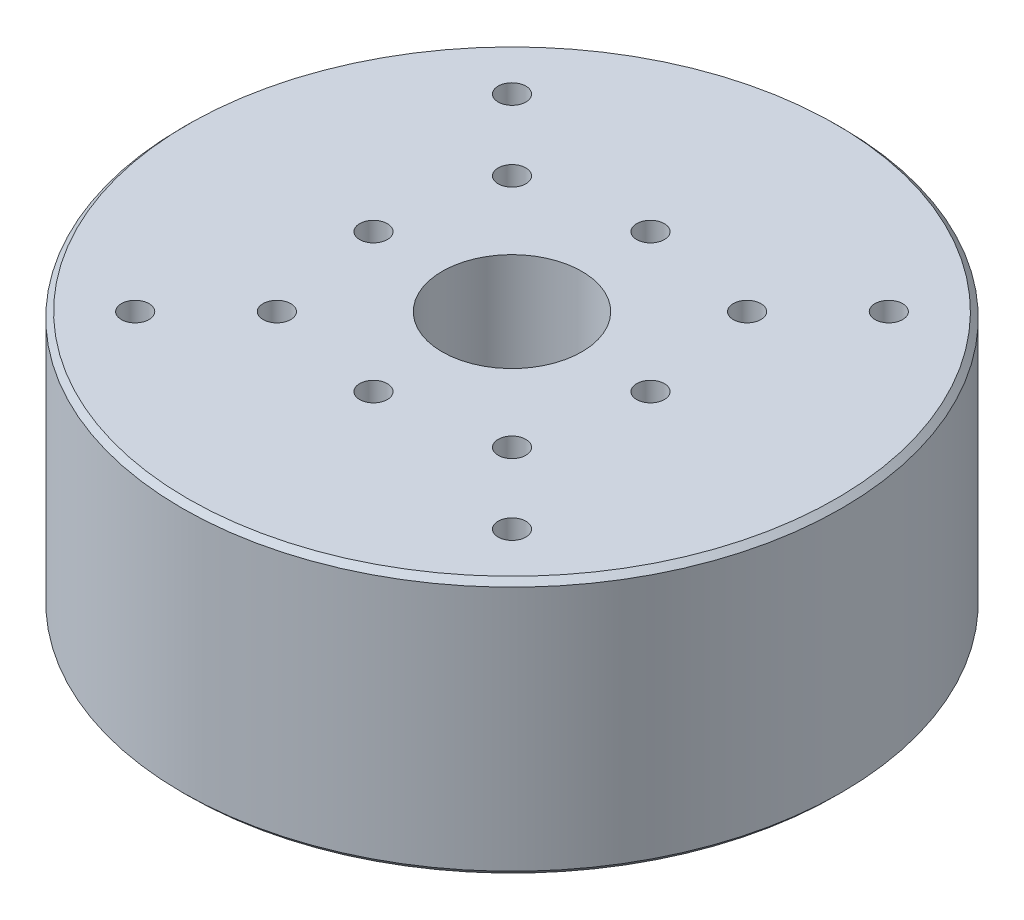
SolidWorks part; units mm, degrees
ref_plane "Front Plane" through (0, 0, 0) normal (0, 0, 1) x (1, 0, 0)
ref_plane "Top Plane" through (0, 0, 0) normal (0, 1, 0) x (1, 0, 0)
ref_plane "Right Plane" through (0, 0, 0) normal (1, 0, 0) x (0, 0, -1)
sketch "Sketch1" plane through (0, 0, 0) normal (0, 1, 0) x (1, 0, 0)
  circle A0 centre (0, 0) radius 29.75
  dimension "D1" = 59.5
extrude "Boss-Extrude1" add sketch "Sketch1" along normal blind 23.2
sketch "Sketch2" plane through (0, 23.2, 0) normal (0, 1, 0) x (1, 0, 0)
  circle A0 centre (0, 0) radius 6.3
  dimension "D1" = 12.6
extrude "Cut-Extrude1" cut sketch "Sketch2" against normal blind 20.5
sketch "Sketch3" plane through (0, 0, 0) normal (0, -1, 0) x (1, 0, 0)
  circle A0 centre (0, 0) radius 4.75
  dimension "D1" = 9.5
extrude "Cut-Extrude2" cut sketch "Sketch3" against normal up to surface (2.7 mm away) up to face at (0, 2.7, 6.3)
chamfer "Chamfer1" distance 0.5 angle 45 2 edges at (0, 0, 29.75) (0, 23.2, 29.75)
hole_wizard "M3x0.5 Tapped Hole1" positions "Sketch4" profile "Sketch5" tap size "M3x0.5" standard "ANSI Metric"
sketch "Sketch4" plane through (0, 0, 0) normal (0, -1, 0) x (-1, 0, 0)
  line L0 (0, 0) -> (0, 22) construction
  point P2 (0, 22)
  dimension "D1" = 22
sketch "Sketch5" plane through (0, 0, -22) normal (1, 0, 0) x (0, 0, -1)
  line L0 (0, 0) -> (0, 5.7511)
  line L1 (0, 5.7511) -> (1.25, 5)
  line L2 (1.25, 5) -> (1.25, 0)
  line L5 (1.25, 0) -> (0, 0)
  line L10 (0, 5.7511) -> (-1.25, 5) construction
  line L11 (0, -6.35) -> (0, 107.95) construction
  dimension "Tap Drill Dia." = 2.5
  dimension "Tap Drill Depth" = 5
  dimension "Drill Angle" = 118
cosmetic thread "Hole Thread1" parameters "D1"=6, "D2"=3
pattern_circular "CirPattern1" count 7 every 45 about axis through (0, 0, 0) along (0, 1, 0) of "M3x0.5 Tapped Hole1"
cosmetic thread "Hole Thread2" parameters "D1"=6, "D2"=3
cosmetic thread "Hole Thread3" parameters "D1"=6, "D2"=3
cosmetic thread "Hole Thread4" parameters "D1"=6, "D2"=3
cosmetic thread "Hole Thread5" parameters "D1"=6, "D2"=3
cosmetic thread "Hole Thread6" parameters "D1"=6, "D2"=3
cosmetic thread "Hole Thread7" parameters "D1"=6, "D2"=3
hole_wizard "M3x0.5 Tapped Hole2" positions "Sketch6" profile "Sketch7" tap size "M3x0.5" standard "ANSI Metric"
sketch "Sketch6" plane through (0, 0, 0) normal (0, -1, 0) x (-1, 0, 0)
  line L0 (0, 0) -> (8.8388, 8.8388) construction
  line L2 (0, 0) -> (14.7072, 0) construction
  point P2 (8.8388, 8.8388)
  dimension "D1" = 12.5
  dimension "D2" = 45
sketch "Sketch7" plane through (-8.8388, 0, -8.8388) normal (1, 0, 0) x (0, 0, -1)
  line L0 (0, 0) -> (0, 5.7511)
  line L1 (0, 5.7511) -> (1.25, 5)
  line L2 (1.25, 5) -> (1.25, 0)
  line L5 (1.25, 0) -> (0, 0)
  line L10 (0, 5.7511) -> (-1.25, 5) construction
  line L11 (0, -6.35) -> (0, 107.95) construction
  dimension "Tap Drill Dia." = 2.5
  dimension "Tap Drill Depth" = 5
  dimension "Drill Angle" = 118
cosmetic thread "Hole Thread8" parameters "D1"=6, "D2"=3
pattern_circular "CirPattern2" count 4 every 90 about axis through (0, 0, 0) along (0, 1, 0) of "M3x0.5 Tapped Hole2"
cosmetic thread "Hole Thread9" parameters "D1"=6, "D2"=3
cosmetic thread "Hole Thread10" parameters "D1"=6, "D2"=3
cosmetic thread "Hole Thread11" parameters "D1"=6, "D2"=3
hole_wizard "M3x0.5 Tapped Hole3" positions "Sketch8" profile "Sketch9" tap size "M3x0.5" standard "ANSI Metric"
sketch "Sketch8" plane through (0, 0, 0) normal (0, -1, 0) x (-1, 0, 0)
  line L0 (0, 0) -> (15, 0) construction
  point P0 (15, 0)
  dimension "D1" = 15
sketch "Sketch9" plane through (-15, 0, 0) normal (1, 0, 0) x (0, 0, -1)
  line L0 (0, 0) -> (0, 5.7511)
  line L1 (0, 5.7511) -> (1.25, 5)
  line L2 (1.25, 5) -> (1.25, 0)
  line L5 (1.25, 0) -> (0, 0)
  line L10 (0, 5.7511) -> (-1.25, 5) construction
  line L11 (0, -6.35) -> (0, 107.95) construction
  dimension "Tap Drill Dia." = 2.5
  dimension "Tap Drill Depth" = 5
  dimension "Drill Angle" = 118
cosmetic thread "Hole Thread12" parameters "D1"=6, "D2"=3
pattern_circular "CirPattern3" count 4 every 90 about axis through (0, 0, 0) along (0, 1, 0) of "M3x0.5 Tapped Hole3"
cosmetic thread "Hole Thread13" parameters "D1"=6, "D2"=3
cosmetic thread "Hole Thread14" parameters "D1"=6, "D2"=3
cosmetic thread "Hole Thread15" parameters "D1"=6, "D2"=3
sketch "Sketch10" plane through (0, 0, 0) normal (0, -1, 0) x (1, 0, 0)
  line L0 (-20.1166, -13.8158) -> (-13.0455, -20.8869)
  line L1 (-13.0455, -20.8869) -> (-15.8739, -23.7153)
  line L2 (-15.8739, -23.7153) -> (-22.945, -16.6442)
  line L3 (-22.945, -16.6442) -> (-20.1166, -13.8158)
  line L4 (-16.581, -17.3514) -> (0, 0) construction
  point P7 (-16.5412, -22.1766)
  dimension "D1" = 10
  dimension "D2" = 4
  dimension "D3" = 24
extrude "Cut-Extrude3" cut sketch "Sketch10" against normal blind 5
fillet "Fillet1" radius 0.5 4 edges at (-13.0455, 2.5, -20.8869) (-20.1166, 2.5, -13.8158) (-22.945, 2.5, -16.6442) (-15.8739, 2.5, -23.7153)
hole_wizard "M3x0.5 Tapped Hole4" positions "Sketch11" profile "Sketch12" tap size "M3x0.5" standard "ANSI Metric"
sketch "Sketch11" plane through (0, 23.2, 0) normal (0, 1, 0) x (1, 0, 0)
  line L0 (17, -17) -> (17, 17) construction
  line L1 (17, 17) -> (-17, 17) construction
  line L2 (-17, 17) -> (-17, -17) construction
  line L3 (-17, -17) -> (17, -17) construction
  line L5 (17, -17) -> (-17, 17) construction
  point P0 (-17, 17)
  point P2 (-17, -17)
  point P4 (17, -17)
  point P6 (17, 17)
  point P24 (0, 0)
  dimension "D1" = 34
  dimension "D2" = 34
sketch "Sketch12" plane through (-17, 23.2, -17) normal (1, 0, 0) x (0, 0, 1)
  line L0 (0, 0) -> (0, 5.7511)
  line L1 (0, 5.7511) -> (1.25, 5)
  line L2 (1.25, 5) -> (1.25, 0)
  line L5 (1.25, 0) -> (0, 0)
  line L10 (0, 5.7511) -> (-1.25, 5) construction
  line L11 (0, -6.35) -> (0, 107.95) construction
  dimension "Tap Drill Dia." = 2.5
  dimension "Tap Drill Depth" = 5
  dimension "Drill Angle" = 118
cosmetic thread "Hole Thread16" parameters "D1"=6, "D2"=3
cosmetic thread "Hole Thread17" parameters "D1"=6, "D2"=3
cosmetic thread "Hole Thread18" parameters "D1"=6, "D2"=3
cosmetic thread "Hole Thread19" parameters "D1"=6, "D2"=3
hole_wizard "M3x0.5 Tapped Hole5" positions "Sketch13" profile "Sketch14" tap size "M3x0.5" standard "ANSI Metric"
sketch "Sketch13" plane through (0, 23.2, 0) normal (0, 1, 0) x (1, 0, 0)
  line L0 (0, 0) -> (12.5, 0) construction
  line L3 (0, 0) -> (10.6066, 10.6066) construction
  point P0 (12.5, 0)
  point P2 (10.6066, 10.6066)
  dimension "D1" = 45
  dimension "D2" = 12.5
  dimension "D3" = 15
sketch "Sketch14" plane through (12.5, 23.2, 0) normal (1, 0, 0) x (0, 0, 1)
  line L0 (0, 0) -> (0, 5.7511)
  line L1 (0, 5.7511) -> (1.25, 5)
  line L2 (1.25, 5) -> (1.25, 0)
  line L5 (1.25, 0) -> (0, 0)
  line L10 (0, 5.7511) -> (-1.25, 5) construction
  line L11 (0, -6.35) -> (0, 107.95) construction
  dimension "Tap Drill Dia." = 2.5
  dimension "Tap Drill Depth" = 5
  dimension "Drill Angle" = 118
cosmetic thread "Hole Thread20" parameters "D1"=6, "D2"=3
cosmetic thread "Hole Thread21" parameters "D1"=6, "D2"=3
pattern_circular "CirPattern4" count 4 every 90 about axis through (0, 0, 0) along (0, 1, 0) of "M3x0.5 Tapped Hole5"
cosmetic thread "Hole Thread22" parameters "D1"=6, "D2"=3
cosmetic thread "Hole Thread23" parameters "D1"=6, "D2"=3
cosmetic thread "Hole Thread24" parameters "D1"=6, "D2"=3
cosmetic thread "Hole Thread25" parameters "D1"=6, "D2"=3
cosmetic thread "Hole Thread26" parameters "D1"=6, "D2"=3
cosmetic thread "Hole Thread27" parameters "D1"=6, "D2"=3
equation "\"D2@Sketch11\"=\"D1@Sketch11\""
